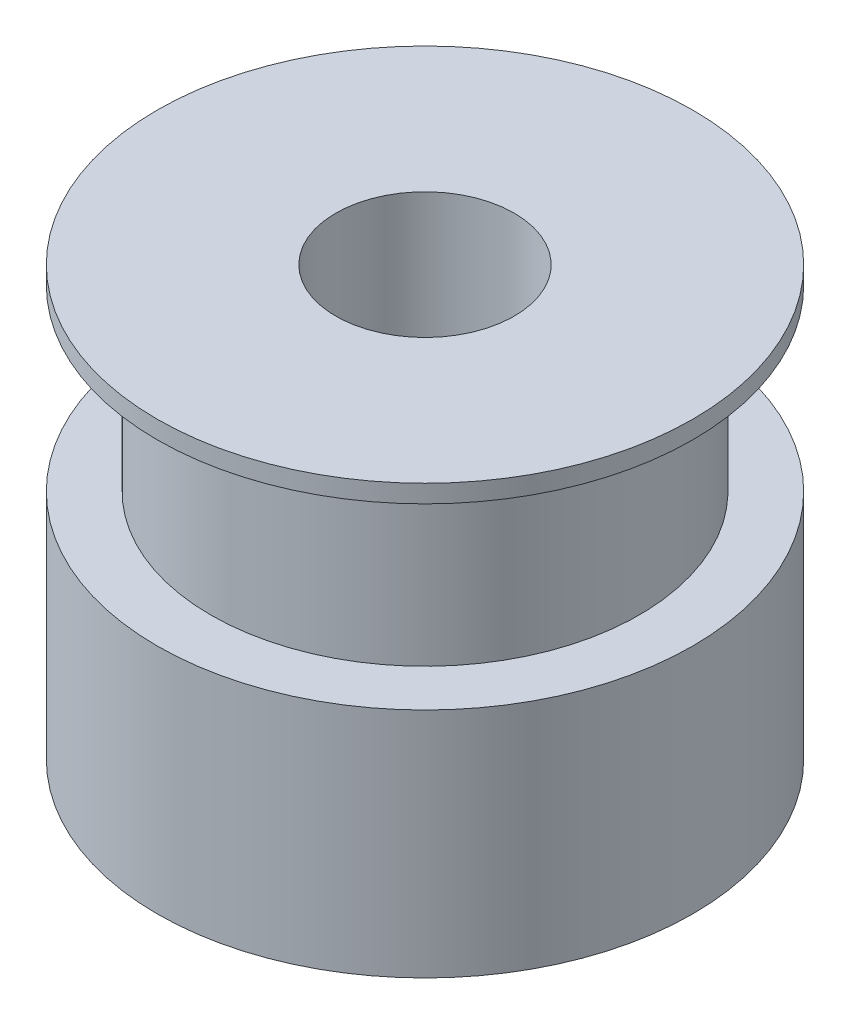
SolidWorks part; units mm, degrees
material "1060 Alloy"
ref_plane "Front Plane" through (0, 0, 0) normal (0, 0, 1) x (1, 0, 0)
ref_plane "Top Plane" through (0, 0, 0) normal (0, 1, 0) x (1, 0, 0)
ref_plane "Right Plane" through (0, 0, 0) normal (1, 0, 0) x (0, 0, -1)
sketch "Sketch1" plane through (0, 0, 0) normal (0, 0, 1) x (1, 0, 0)
  line L0 (-2.5, -12) -> (-2.5, 0)
  line L1 (-2.5, 0) -> (-7.5, 0)
  line L2 (-7.5, 0) -> (-7.5, -0.5)
  line L3 (-7.5, -0.5) -> (-6, -0.5)
  line L4 (-6, -0.5) -> (-6, -5.5)
  line L5 (-6, -5.5) -> (-7.5, -5.5)
  line L6 (-7.5, -5.5) -> (-7.5, -12)
  line L9 (-7.5, -12) -> (-2.5, -12)
  line L10 (0, -5.5965) -> (0, 11.7984) construction
  dimension "D1" = 2.5
  dimension "D2" = 7.5
  dimension "D3" = 12
  dimension "D4" = 0.5
  dimension "D5" = 5
  dimension "D6" = 3.5
revolve "Revolve1" add sketch "Sketch1" angle 360 about L10
